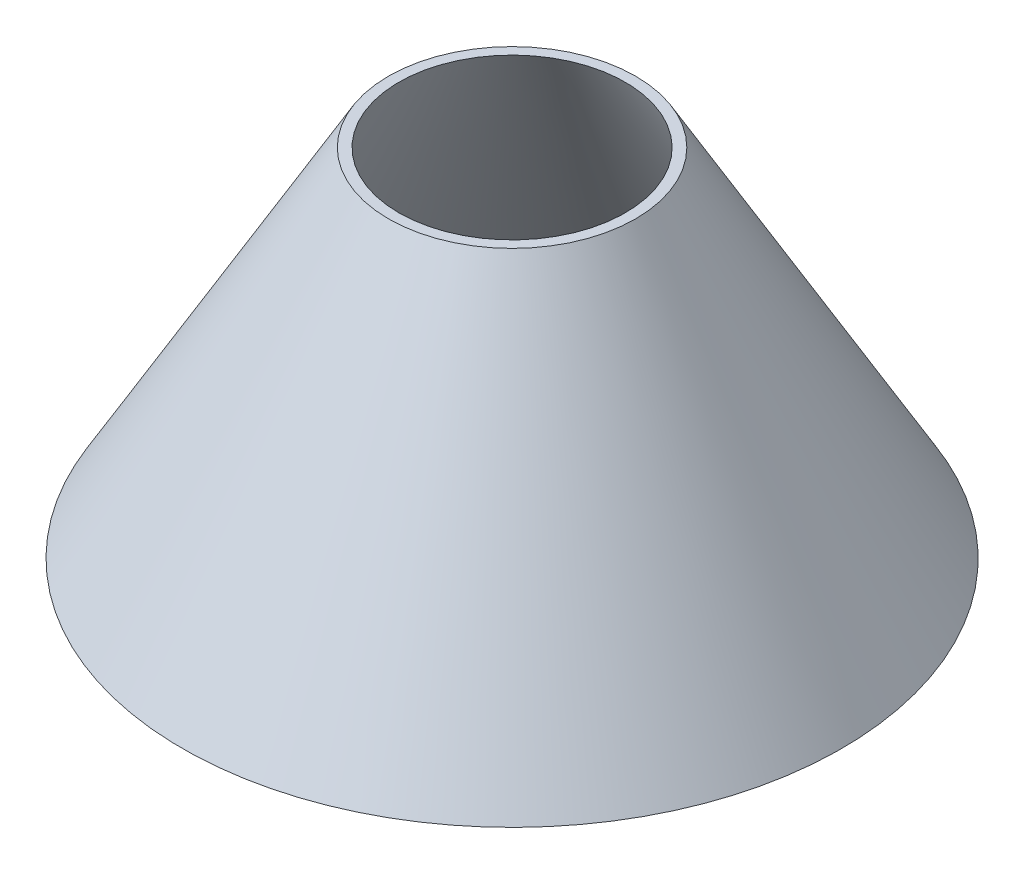
SolidWorks part; units mm, degrees
ref_plane "Front Plane" through (0, 0, 0) normal (0, 0, 1) x (1, 0, 0)
ref_plane "Top Plane" through (0, 0, 0) normal (0, 1, 0) x (1, 0, 0)
ref_plane "Right Plane" through (0, 0, 0) normal (1, 0, 0) x (0, 0, -1)
sketch "Sketch1" plane through (0, 0, 0) normal (0, 0, 1) x (1, 0, 0)
  line L0 (-44, 0) -> (44, 0)
  line L1 (0, 0) -> (0, 47.5) construction
  line L2 (-16.5, 47.5) -> (16.5, 47.5)
  line L3 (-16.5, 47.5) -> (-44, 0)
  line L4 (16.5, 47.5) -> (44, 0)
  point P4 (0, 0)
  point P10 (0, 47.5)
  dimension "D1" = 88
  dimension "D2" = 33
  dimension "D3" = 47.5
revolve "Revolve1" add sketch "Sketch1" angle 360 about L1
shell "Shell4" thickness 1.2
